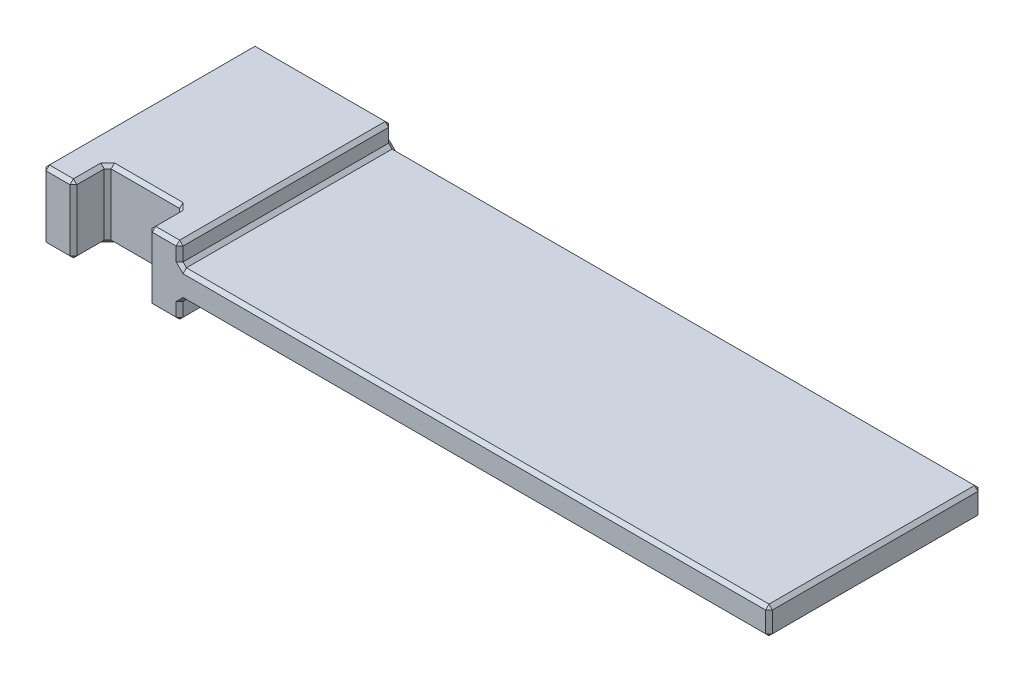
SolidWorks part; units mm, degrees
ref_plane "Front Plane" through (0, 0, 0) normal (0, 0, 1) x (1, 0, 0)
ref_plane "Top Plane" through (0, 0, 0) normal (0, 1, 0) x (1, 0, 0)
ref_plane "Right Plane" through (0, 0, 0) normal (1, 0, 0) x (0, 0, -1)
sketch "Sketch1" plane through (0, 0, 0) normal (0, 1, 0) x (1, 0, 0)
  line L1 (0, 0) -> (106, 0)
  line L2 (0, 0) -> (0, 31)
  line L3 (0, 31) -> (106, 31)
  line L4 (106, 0) -> (106, 31)
  dimension "D1" = 106
  dimension "D2" = 31
extrude "Boss-Extrude1" add sketch "Sketch1" along normal blind 4
ref_plane "Plane1" through (0, 2, 0) normal (0, 1, 0) x (1, 0, 0)
sketch "Sketch2" plane through (0, 2, 0) normal (0, 1, 0) x (1, 0, 0)
  line L0 (0, 0) -> (106, 0) construction
  line L1 (0, 31) -> (20, 31)
  line L2 (0, 31) -> (0, 0)
  line L3 (0, 0) -> (20, 0)
  line L4 (20, 31) -> (20, 0)
  dimension "D1" = 20
extrude "Boss-Extrude2" add sketch "Sketch2" along normal mid plane 10
sketch "Sketch3" plane through (0, 7, 0) normal (0, 1, 0) x (1, 0, 0)
  line L0 (0, 0) -> (20, 0) construction
  line L1 (4.5, 0) -> (15.5, 0)
  line L2 (4.5, 0) -> (4.5, 5)
  line L3 (4.5, 5) -> (15.5, 5)
  line L4 (15.5, 0) -> (15.5, 5)
  line L5 (20, 31) -> (0, 31) construction
  point P8 (10, 31)
  point P9 (10, 5)
  dimension "D1" = 5
  dimension "D2" = 11
extrude "Cut-Extrude1" cut sketch "Sketch3" against normal through all
chamfer "Chamfer1" distance 0.5 angle 45 36 edges at (106, 4, -15.5) (63, 0, 0) (20, 0, -15.5) (63, 4, 0) (63, 4, -31) (20, 5.5, 0) (20, 4, -15.5) (20, 5.5, -31) (0, -3, -15.5) (2.25, -3, 0) (20, -1.5, 0) (20, -3, -15.5) (20, -1.5, -31) (10, -3, -31) (0, 7, -15.5) (2.25, 7, 0) (20, 7, -15.5) (10, 7, -31) (17.75, 7, 0) (17.75, -3, 0) (4.5, -3, -2.5) (4.5, 2, 0) (10, -3, -5) (4.5, 2, -5) (15.5, -3, -2.5) (15.5, 2, -5) (15.5, 2, 0) (4.5, 7, -2.5) (15.5, 7, -2.5) (10, 7, -5) (63, 0, -31) (106, 0, -15.5) (0, 2, -31) (106, 2, -31) (106, 2, 0) (0, 2, 0)
